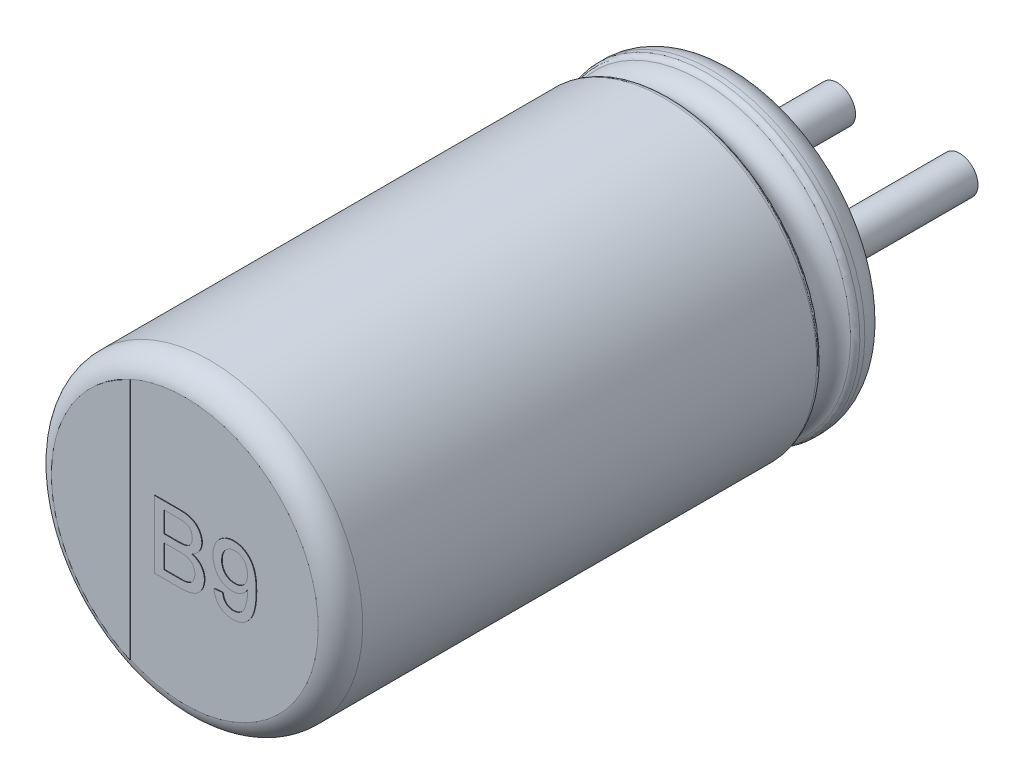
SolidWorks part; units mm, degrees
ref_plane "Plan de face" through (0, 0, 0) normal (0, 0, 1) x (1, 0, 0)
ref_plane "Plan de dessus" through (0, 0, 0) normal (0, 1, 0) x (1, 0, 0)
ref_plane "Plan de droite" through (0, 0, 0) normal (1, 0, 0) x (0, 0, -1)
sketch "Sketch10" plane through (0, 0, 0) normal (1, 0, 0) x (0, 0, -1)
  line L0 (18.1631, 0) -> (-18.9631, 0) construction
  line L1 (-9, 0) -> (-0.05, 0)
  line L2 (-9, 0) -> (-9, 2.1736)
  line L3 (-8.6, 2.5) -> (-1.1846, 2.5)
  line L4 (-0.05, 1.9031) -> (-0.05, 0)
  line L7 (-0.4794, 2.5) -> (-0.3982, 2.5)
  arc A0 (-9, 2.1736) -> (-8.6, 2.5) centre (-8.6068, 2.1001) cw
  arc A1 (-0.3982, 2.5) -> (-0.05, 1.9031) centre (-0.3982, 2.1) cw
  arc A2 (-0.5713, 2.4394) -> (-1.0926, 2.4394) centre (-0.832, 2.551) cw
  arc A3 (-1.0926, 2.4394) -> (-1.1846, 2.5) centre (-1.1846, 2.4) ccw
  arc A4 (-0.5713, 2.4394) -> (-0.4794, 2.5) centre (-0.4794, 2.4) cw
  point P4 (0.57, -0.65)
  point P13 (-9, 2.5)
  dimension "D2" = 0.4
  dimension "D3" = 0.4
  dimension "D4" = 0.1
  dimension "D5" = 0.1
  dimension "D1" = 2.5
  dimension "D7" = 0.05
  dimension "D8" = 2.5
revolve "Повернуть1" add sketch "Sketch10" angle 360 about L0
sketch "Эскиз2" plane through (0, 0, 0.05) normal (0, 0, -1) x (-1, 0, 0)
  line L1 (0, 0.7993) -> (0, -1.0496) construction
  line L2 (-1, 0) -> (3.8813, 0) construction
  circle A3 centre (-1, 0) radius 0.3
  circle A7 centre (1, 0) radius 0.3
  dimension "D1" = 2
extrude "Бобышка-Вытянуть1" add sketch "Эскиз2" along normal blind 2.7
sketch "Эскиз4" plane through (0, 0, 9) normal (0, 0, 1) x (1, 0, 0)
  line L0 (-0.8932, -1.9816) -> (-0.8932, 1.9816)
  circle A1 centre (0, 0) radius 2.1736 construction
  arc A2 (-0.8932, 1.9816) -> (-0.8932, -1.9816) centre (0, 0) ccw
extrude "Бобышка-Вытянуть2" add sketch "Эскиз4" along normal blind 0.01
sketch "Эскиз5" plane through (0, 0, 9) normal (0, 0, 1) x (1, 0, 0)
  text T0 "B9" font "Arial" height 1.1
extrude "Текст" add sketch "Эскиз5" along normal blind 0.01
sketch "Эскиз6" plane through (0, 0, 0.05) normal (0, 0, -1) x (-1, 0, 0)
  line L0 (-1, 0.4) -> (-1.3519, 0.4)
  line L1 (-1, -0.4) -> (-1.3519, -0.4)
  line L2 (1, -0.4) -> (1.3519, -0.4)
  line L3 (1, 0.4) -> (1.3519, 0.4)
  arc A0 (-1.5772, -0.7583) -> (1.5772, -0.7583) centre (0, 0) ccw
  arc A1 (-1, -0.4) -> (-1, 0.4) centre (-1, 0) ccw
  arc A2 (1, 0.4) -> (1, -0.4) centre (1, 0) ccw
  arc A3 (1.5772, 0.7583) -> (-1.5772, 0.7583) centre (0, 0) ccw
  arc A4 (1.3519, 0.4) -> (1.5772, 0.7583) centre (1.3519, 0.65) ccw
  arc A5 (1.3519, -0.4) -> (1.5772, -0.7583) centre (1.3519, -0.65) cw
  arc A6 (-1.5772, -0.7583) -> (-1.3519, -0.4) centre (-1.3519, -0.65) cw
  arc A7 (-1.3519, 0.4) -> (-1.5772, 0.7583) centre (-1.3519, 0.65) cw
  point P7 (1.7037, 0.4)
  point P23 (0, -1.75)
  point P24 (0, 1.75)
  dimension "D1" = 0.25
  dimension "D2" = 3.5
extrude "Бобышка-Вытянуть5" add sketch "Эскиз6" along normal blind 0.05 contours A3 A7 L0 A1 L1 A6 A0 A5 L2 A2 L3 A4
